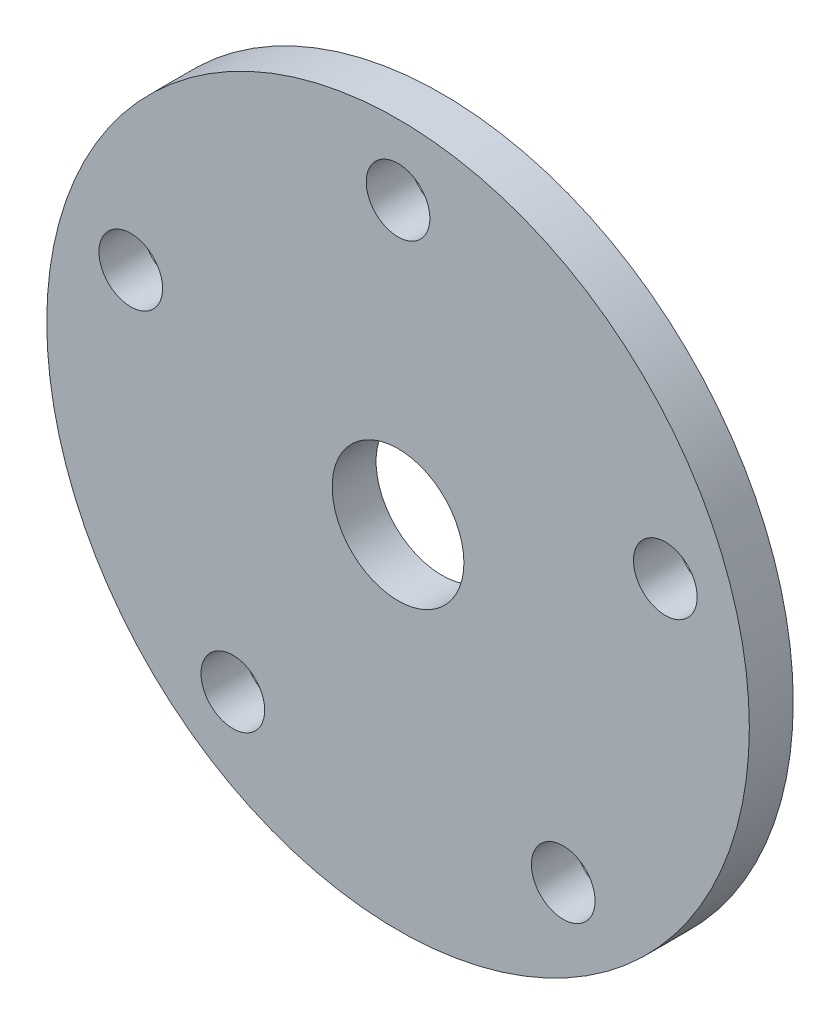
SolidWorks part; units mm, degrees
material "1.0038 (S235JRG2)"
ref_plane "Plan de face" through (0, 0, 0) normal (0, 0, 1) x (1, 0, 0)
ref_plane "Plan de dessus" through (0, 0, 0) normal (0, 1, 0) x (1, 0, 0)
ref_plane "Plan de droite" through (0, 0, 0) normal (1, 0, 0) x (0, 0, -1)
sketch "Esquisse1" plane through (0, 0, 0) normal (0, 0, 1) x (1, 0, 0)
  circle A0 centre (0, 0) radius 80
  circle A2 centre (0, 0) radius 15
  dimension "D1" = 30
  dimension "D3" = 160
extrude "Boss.-Extru.1" add sketch "Esquisse1" along normal mid plane 10
sketch "Esquisse3" plane through (0, 0, 5) normal (0, 0, 1) x (1, 0, 0)
  circle A0 centre (0, 64) radius 7.25
  circle A1 centre (0, 0) radius 64
  dimension "D1" = 14.5
  dimension "D2" = 128
extrude "Enlèv. mat.-Extru.1" cut sketch "Esquisse3" against normal blind 10 contours A0
pattern_circular "Répétition circulaire4" count 5 over 360 about axis through (0, 0, 0) along (0, 0, 1) of "Enlèv. mat.-Extru.1"
